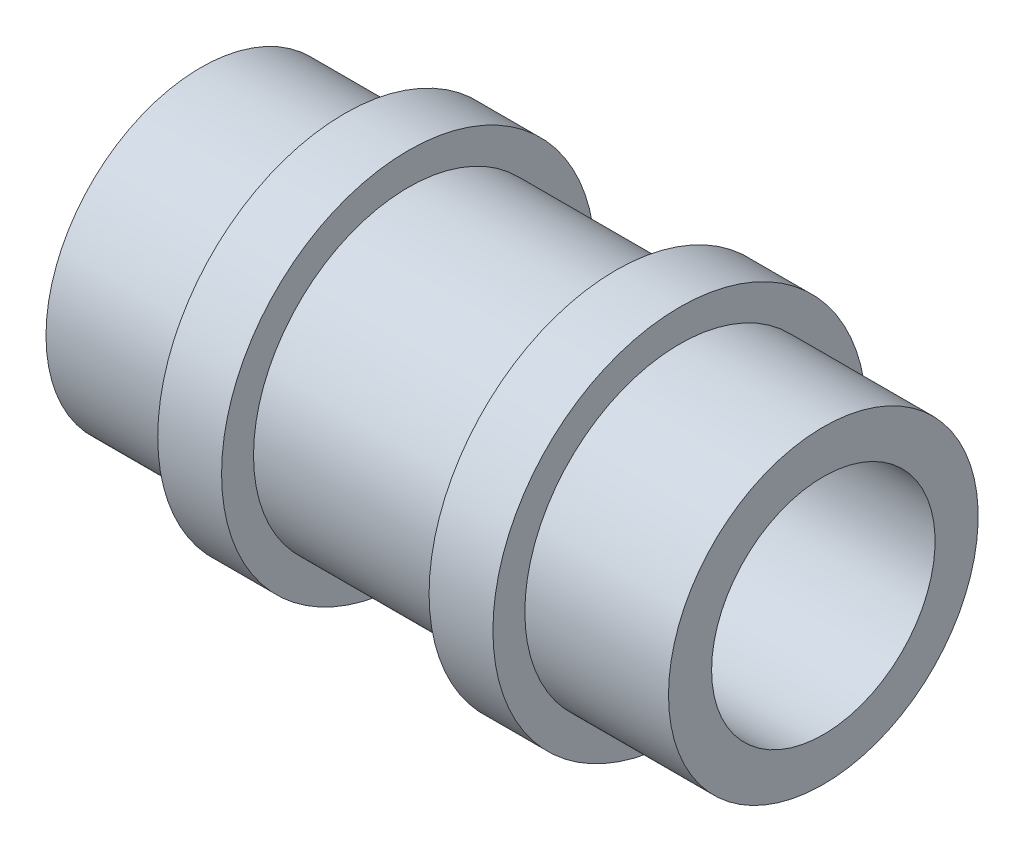
SolidWorks part; units mm, degrees
ref_plane "Přední rovina" through (0, 0, 0) normal (0, 0, 1) x (1, 0, 0)
ref_plane "Vrchní rovina" through (0, 0, 0) normal (0, 1, 0) x (1, 0, 0)
ref_plane "Pravá rovina" through (0, 0, 0) normal (1, 0, 0) x (0, 0, -1)
sketch "Skica1" plane through (0, 0, 0) normal (0, 0, 1) x (1, 0, 0)
  line L0 (0, 0) -> (19.314, 0) construction
  line L1 (0, 3.5) -> (9.75, 3.5)
  line L2 (9.75, 3.5) -> (9.75, 4.85)
  line L3 (9.75, 4.85) -> (5.25, 4.85)
  line L4 (5.25, 4.85) -> (5.25, 5.85)
  line L5 (5.25, 5.85) -> (3.25, 5.85)
  line L6 (3.25, 5.85) -> (3.25, 4.85)
  line L7 (3.25, 4.85) -> (-3.25, 4.85)
  line L8 (-3.25, 4.85) -> (-3.25, 5.85)
  line L9 (-3.25, 5.85) -> (-5.25, 5.85)
  line L10 (-5.25, 5.85) -> (-5.25, 4.85)
  line L11 (-5.25, 4.85) -> (-9.75, 4.85)
  line L12 (-9.75, 4.85) -> (-9.75, 3.5)
  line L13 (-9.75, 3.5) -> (0, 3.5)
  line L14 (0, 4.85) -> (0, 3.5) construction
  line L15 (0, 3.5) -> (0, 0) construction
  dimension "D1" = 19.5
  dimension "D2" = 6.5
  dimension "D3" = 2
  dimension "D4" = 2
  dimension "D5" = 9.7
  dimension "D6" = 7
  dimension "D7" = 1
revolve "Rotovat1" add sketch "Skica1" angle 360 about L0
